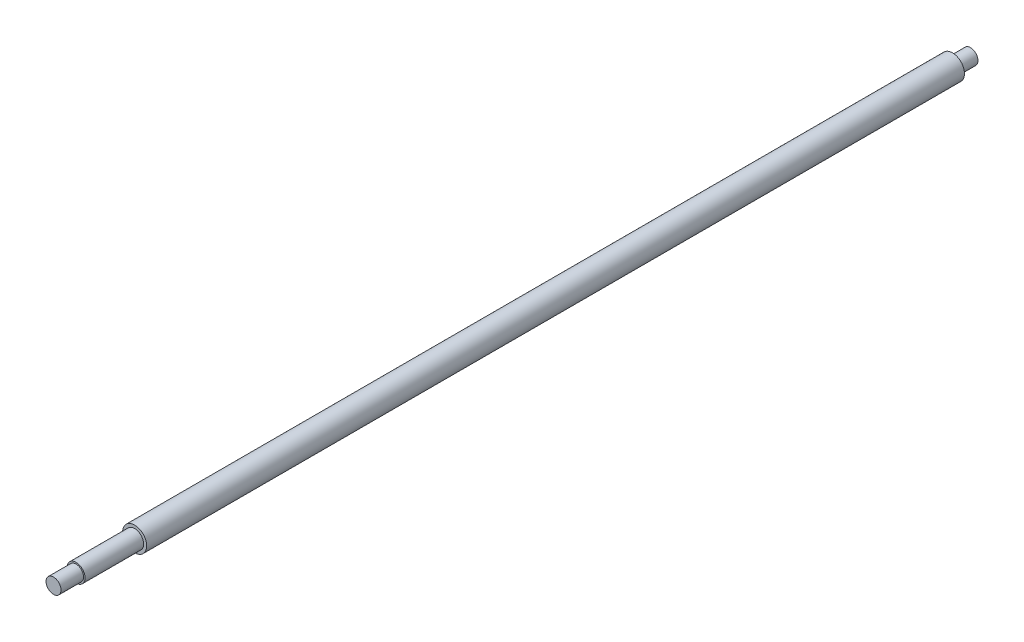
SolidWorks part; units mm, degrees
material "1060 Alloy"
ref_plane "Front Plane" through (0, 0, 0) normal (0, 0, 1) x (1, 0, 0)
ref_plane "Top Plane" through (0, 0, 0) normal (0, 1, 0) x (1, 0, 0)
ref_plane "Right Plane" through (0, 0, 0) normal (1, 0, 0) x (0, 0, -1)
sketch "Sketch1" plane through (0, 0, 0) normal (1, 0, 0) x (0, 0, -1)
  line L0 (0, 0) -> (-42.623, 0) construction
  line L1 (-610.5, 0) -> (-610.5, 5)
  line L2 (-610.5, 5) -> (-595.5, 5)
  line L3 (-595.5, 5) -> (-595.5, 6)
  line L4 (-595.5, 6) -> (-556.5, 6)
  line L5 (-556.5, 6) -> (-556.5, 8)
  line L6 (-556.5, 8) -> (-12, 8)
  line L7 (-12, 8) -> (-12, 5)
  line L8 (-12, 5) -> (0, 5)
  line L9 (0, 5) -> (0, 0)
  line L10 (-610.5, 0) -> (0, 0)
  dimension "D1" = 5
  dimension "D2" = 6
  dimension "D3" = 8
  dimension "D4" = 5
  dimension "D5" = 12
  dimension "D6" = 39
  dimension "D7" = 15
  dimension "D8" = 544.5
revolve "Revolve1" add sketch "Sketch1" angle 360 about L0
sketch "Sketch3" [suppressed] plane through (0, 0, 0) normal (1, 0, 0) x (0, 0, -1)
  line L0 (-80.9254, 0) -> (-123.5483, 0) construction
  line L1 (-275.75, 0) -> (-275.75, 5)
  line L2 (-275.75, 5) -> (-260.75, 5)
  line L3 (-260.75, 5) -> (-260.75, 6)
  line L4 (-260.75, 6) -> (-221.75, 6)
  line L5 (-221.75, 6) -> (-221.75, 8)
  line L6 (-221.75, 8) -> (-12, 8)
  line L7 (-12, 8) -> (-12, 5)
  line L8 (-12, 5) -> (0, 5)
  line L9 (0, 5) -> (0, 0)
  line L10 (-275.75, 0) -> (0, 0)
  dimension "D1" = 10
  dimension "D2" = 6
  dimension "D3" = 8
  dimension "D4" = 10
  dimension "D5" = 15
  dimension "D6" = 39
  dimension "D7" = 209.75
  dimension "D8" = 12
revolve "Revolve2" [suppressed] add sketch "Sketch3" angle 360 about L0
